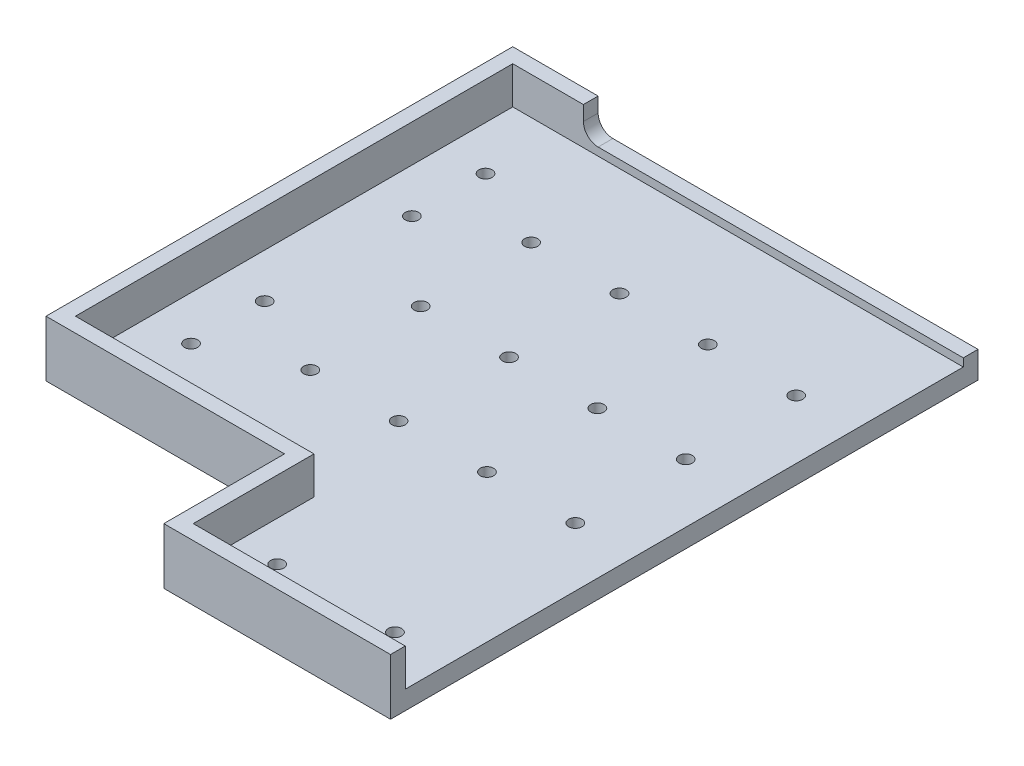
SolidWorks part; units mm, degrees
ref_plane "Front Plane" through (0, 0, 0) normal (0, 0, 1) x (1, 0, 0)
ref_plane "Top Plane" through (0, 0, 0) normal (0, 1, 0) x (1, 0, 0)
ref_plane "Right Plane" through (0, 0, 0) normal (1, 0, 0) x (0, 0, -1)
sketch "Sketch1" plane through (0, 0, 0) normal (0, 1, 0) x (1, 0, 0)
  line L1 (0, 0) -> (158, 0)
  line L2 (0, 0) -> (0, -199.5)
  line L3 (0, -199.5) -> (158, -199.5)
  line L4 (158, 0) -> (158, -199.5)
  dimension "D1" = 158
  dimension "D2" = 199.5
extrude "Boss-Extrude1" add sketch "Sketch1" along normal blind 6.35
sketch "Sketch2" plane through (0, 6.35, 0) normal (0, 1, 0) x (1, 0, 0)
  line L0 (0, -199.5) -> (158, -199.5) construction
  line L1 (81, -199.5) -> (0, -199.5)
  line L2 (81, -199.5) -> (81, -158.5)
  line L3 (81, -158.5) -> (0, -158.5)
  line L4 (0, -199.5) -> (0, -158.5)
  dimension "D1" = 81
  dimension "D2" = 41
extrude "Cut-Extrude1" cut sketch "Sketch2" against normal through all
sketch "Sketch3" plane through (0, 6.35, 0) normal (0, 1, 0) x (1, 0, 0)
  line L1 (81, -199.5) -> (158, -199.5) construction
  line L6 (81, -199.5) -> (81, -158.5) construction
  line L8 (81, -158.5) -> (0, -158.5) construction
  line L16 (158, 0) -> (158, -5)
  line L17 (158, -199.5) -> (158, 0) construction
  line L18 (158, -5) -> (5, -5)
  line L19 (5, -5) -> (5, -153.5)
  line L20 (5, -153.5) -> (86, -153.5)
  line L21 (86, -153.5) -> (86, -194.5)
  line L23 (0, 0) -> (0, -158.5) construction
  line L24 (158, 0) -> (0, 0) construction
  line L25 (81, -199.5) -> (81, -158.5)
  line L26 (81, -158.5) -> (0, -158.5)
  line L27 (0, 0) -> (0, -158.5)
  line L28 (158, 0) -> (0, 0)
  line L29 (81, -199.5) -> (86, -199.5)
  line L31 (158, -194.5) -> (86, -194.5)
  line L32 (158, -194.5) -> (158, -199.5)
  line L33 (158, -199.5) -> (86, -199.5)
  dimension "D1" = 5
  dimension "D2" = 5
  dimension "D3" = 5
  dimension "D4" = 5
  dimension "D5" = 5
extrude "Boss-Extrude2" add sketch "Sketch3" along normal blind 12.7
sketch "Sketch4" plane through (0, 0, 0) normal (0, -1, 0) x (1, 0, 0)
  line L0 (81, 179.5) -> (158, 179.5) construction
  line L3 (81, 199.5) -> (158, 199.5) construction
  line L4 (119.5, 179.5) -> (119.5, 188.5903) construction
  line L5 (20, 158.5) -> (20, 0) construction
  line L6 (81, 158.5) -> (0, 158.5) construction
  line L7 (158, 0) -> (0, 0) construction
  line L9 (20, 79.25) -> (152.6176, 79.25) construction
  line L10 (158, 199.5) -> (158, 0) construction
  line L11 (81, 199.5) -> (81, 158.5) construction
  line L12 (0, 0) -> (0, 158.5) construction
  point P8 (99.5, 179.5)
  point P11 (139.5, 179.5)
  point P20 (20, 129.25)
  point P21 (20, 104.25)
  point P22 (20, 29.25)
  point P23 (20, 79.25)
  point P24 (20, 54.25)
  dimension "D1" = 20
  dimension "D2" = 40
  dimension "D3" = 20
  dimension "D4" = 25
  dimension "D5" = 25
hole_wizard "M4 Clearance Hole1" positions "Sketch4" profile "Sketch5" hole size "M4" standard "ANSI Metric" end condition up to next
sketch "Sketch5" plane through (20, 0, 54.25) normal (1, 0, 0) x (0, 0, -1)
  line L0 (0, 0) -> (0, 6.35)
  line L1 (0, 6.35) -> (2.25, 6.35)
  line L2 (2.25, 6.35) -> (2.25, 0)
  line L5 (2.25, 0) -> (0, 0)
  line L11 (0, -6.35) -> (0, 107.95) construction
  dimension "Thru Hole Dia." = 4.5
  dimension "Thru Hole Depth" = 6.35
sketch "Sketch7" plane through (0, 0, 0) normal (0, 0, -1) x (-1, 0, 0)
  line L0 (-79, 19.05) -> (-79, 4.7647) construction
  line L2 (-158, 19.05) -> (0, 19.05) construction
  line L3 (-158, 19.05) -> (-29, 19.05)
  line L4 (-158, 19.05) -> (-158, 9.05)
  line L5 (-158, 9.05) -> (-29, 9.05)
  line L6 (-29, 19.05) -> (-29, 9.05)
  line L7 (0, 19.05) -> (0, 0) construction
  line L8 (-158, 19.05) -> (-158, 0) construction
  dimension "D1" = 29
  dimension "D2" = 10
extrude "Cut-Extrude2" cut sketch "Sketch7" against normal up to next
fillet "Fillet1" radius 5 1 edges at (29, 9.05, 2.5)
sketch "Sketch8" plane through (0, 6.35, 0) normal (0, 1, 0) x (1, 0, 0)
  line L0 (158, -116.75) -> (50.5497, -116.75) construction
  line L1 (158, -194.5) -> (158, -5) construction
  line L3 (20, -129.25) -> (20, -104.25) construction
  point P4 (138, -116.75)
  point P15 (20, -116.75)
  dimension "D1" = 20
hole_wizard "M4 Clearance Hole2" positions "Sketch8" profile "Sketch9" hole size "M4" standard "ANSI Metric" end condition up to next
sketch "Sketch9" plane through (138, 6.35, 116.75) normal (1, 0, 0) x (0, 0, 1)
  line L0 (0, 0) -> (0, 6.35)
  line L1 (0, 6.35) -> (2.25, 6.35)
  line L2 (2.25, 6.35) -> (2.25, 0)
  line L5 (2.25, 0) -> (0, 0)
  line L11 (0, -6.35) -> (0, 107.95) construction
  dimension "Thru Hole Dia." = 4.5
  dimension "Thru Hole Depth" = 6.35
pattern_linear "LPattern1" count 4 spacing 30 along (-1, 0, 0) count 3 spacing 37.5 along (0, 0, -1) of "M4 Clearance Hole2"
equation "\"D2@Sketch3\"=\"D1@Sketch3\""
equation "\"D3@Sketch3\"=\"D1@Sketch3\""
equation "\"D4@Sketch3\"=\"D1@Sketch3\""
equation "\"D5@Sketch3\"=\"D1@Sketch3\""
